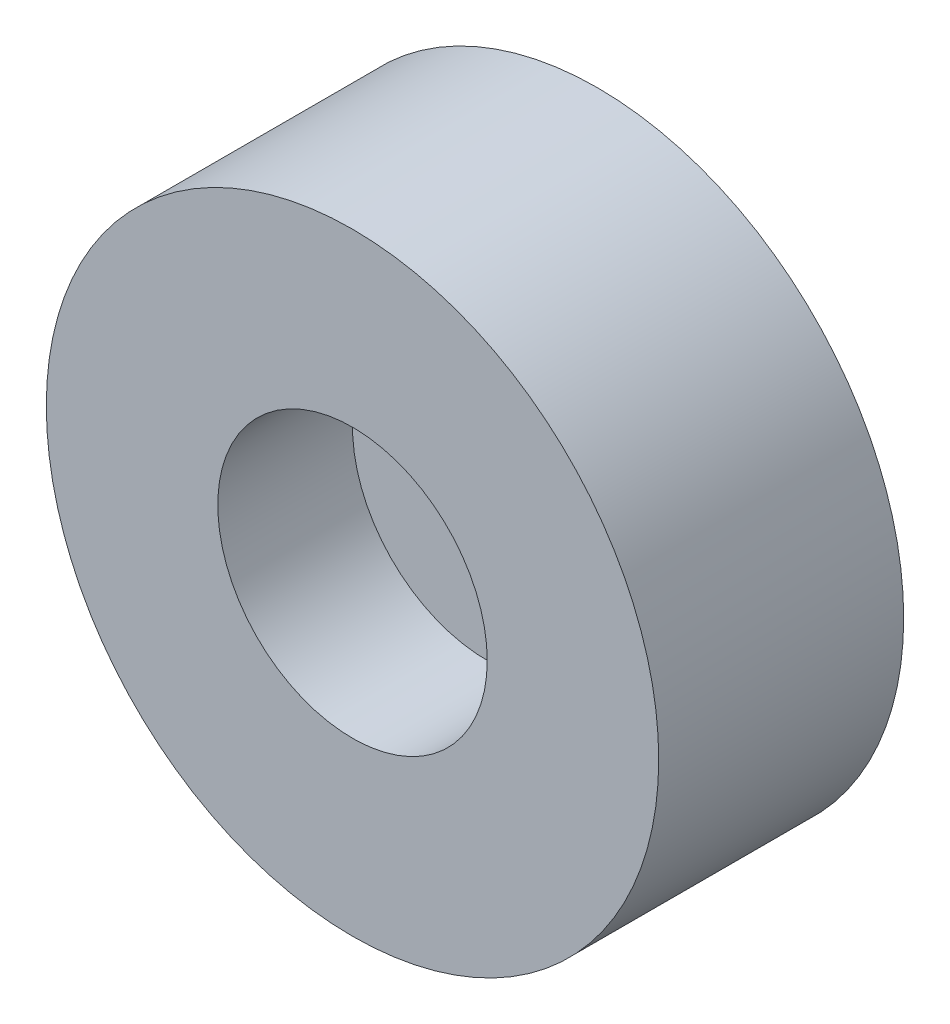
SolidWorks part; units mm, degrees
ref_plane "Front Plane" through (0, 0, 0) normal (0, 0, 1) x (1, 0, 0)
ref_plane "Top Plane" through (0, 0, 0) normal (0, 1, 0) x (1, 0, 0)
ref_plane "Right Plane" through (0, 0, 0) normal (1, 0, 0) x (0, 0, -1)
sketch "Sketch1" plane through (0, 0, 0) normal (0, 0, 1) x (1, 0, 0)
  circle A0 centre (0, 0) radius 6.35
  dimension "D1" = 12.7
extrude "Boss-Extrude1" add sketch "Sketch1" along normal blind 5.08
sketch "Sketch2" plane through (0, 0, 5.08) normal (0, 0, 1) x (1, 0, 0)
  circle A0 centre (0, 0) radius 2.794
  dimension "D1" = 5.588
extrude "Cut-Extrude1" cut sketch "Sketch2" against normal blind 2.794
